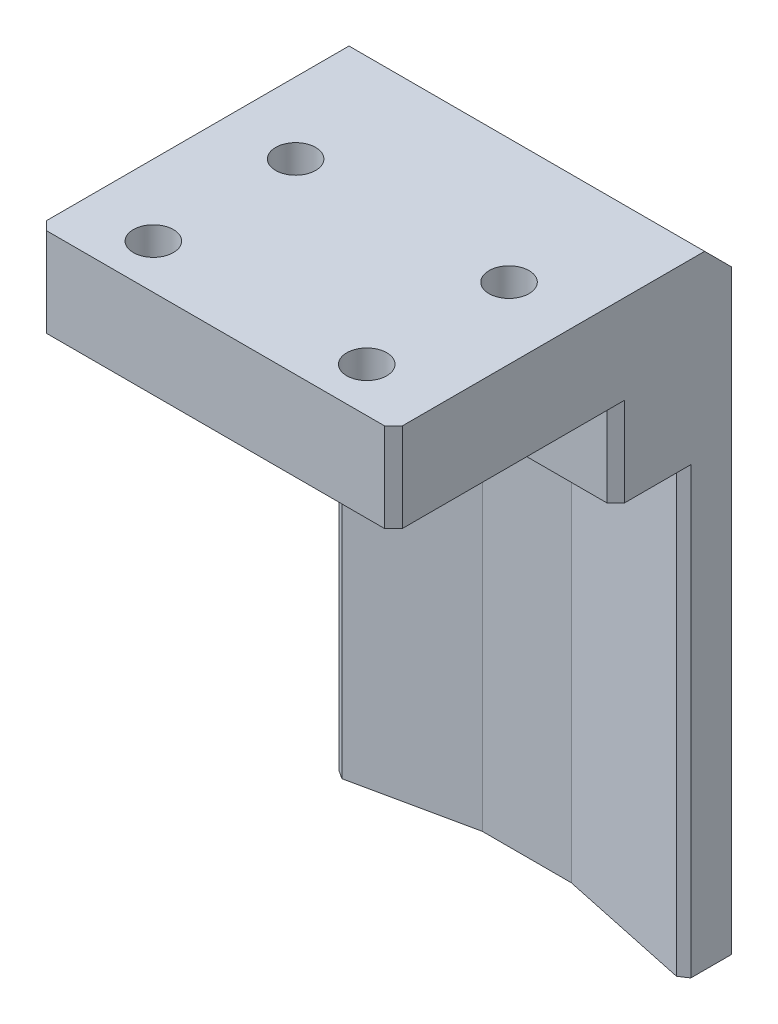
SolidWorks part; units mm, degrees
ref_plane "前视基准面" through (0, 0, 0) normal (0, 0, 1) x (1, 0, 0)
ref_plane "上视基准面" through (0, 0, 0) normal (0, 1, 0) x (1, 0, 0)
ref_plane "右视基准面" through (0, 0, 0) normal (1, 0, 0) x (0, 0, -1)
sketch "草图1" plane through (0, 0, 0) normal (0, 1, 0) x (1, 0, 0)
  line L1 (-20, 7.5) -> (20, 7.5)
  line L2 (-20, 7.5) -> (-20, -7.5)
  line L3 (-20, -7.5) -> (20, -7.5)
  line L4 (20, 7.5) -> (20, -7.5)
  line L5 (-20, 7.5) -> (20, -7.5) construction
  line L6 (-20, -7.5) -> (20, 7.5) construction
  point P0 (0, 0)
  dimension "D1" = 15
  dimension "D2" = 40
extrude "凸台-拉伸1" add sketch "草图1" along normal blind 60
sketch "草图3" plane through (0, 60, 0) normal (0, 1, 0) x (1, 0, 0)
  line L0 (20, -7.5) -> (20, 7.5) construction
  line L1 (-20, 7.5) -> (20, 7.5)
  line L2 (-20, 7.5) -> (-20, -32.5)
  line L3 (-20, -32.5) -> (20, -32.5)
  line L4 (20, 7.5) -> (20, -32.5)
  line L5 (-20, -7.5) -> (20, -7.5) construction
  dimension "D1" = 25
extrude "凸台-拉伸2" add sketch "草图3" along normal blind 10
hole_wizard "M4 六角凹头螺钉的柱形沉头孔1" positions "草图5" profile "草图4" counterbore size "M4" standard "Iso" end condition through all
sketch "草图5" plane through (0, 60, 0) normal (0, -1, 0) x (-1, 0, 0)
  line L0 (0, -32.5) -> (0, 7.5) construction
  line L1 (20, -32.5) -> (-20, -32.5) construction
  line L2 (-20, 7.5) -> (20, 7.5) construction
  point P0 (12, -11.5)
  point P2 (-12, -11.5)
  point P4 (12, -27.5)
  point P6 (-12, -27.5)
  dimension "D1" = 24
  dimension "D2" = 24
  dimension "D3" = 16
  dimension "D4" = 5
sketch "草图4" plane through (-12, 60, 11.5) normal (1, 0, 0) x (0, 0, -1)
  line L0 (0, 0) -> (0, 10)
  line L1 (0, 10) -> (2.25, 10)
  line L3 (2.25, 10) -> (2.25, 4.4)
  line L4 (2.25, 4.4) -> (4, 4.4)
  line L5 (4, 4.4) -> (4, 0)
  line L7 (4, 0) -> (0, 0)
  line L11 (0, -6.35) -> (0, 107.95) construction
  dimension "通孔孔直径" = 4.5
  dimension "通孔孔深度" = 10
  dimension "柱形沉头孔直径" = 8
  dimension "柱形沉头孔深度" = 4.4
chamfer "倒角1" distance 5 angle 45 1 edges at (0, 70, -7.5)
chamfer "倒角2" distance 2 angle 45 2 edges at (20, 32.5, -7.5) (-20, 32.5, -7.5)
sketch "草图7" plane through (0, 0, 0) normal (0, -1, 0) x (1, 0, 0)
  line L0 (-24.6466, 36.5) -> (28.5178, 36.5) construction
  line L1 (18, -7.5) -> (-18, -7.5) construction
  line L2 (0, -7.5) -> (0, 36.5) construction
  line L3 (0, -3.5) -> (25.3434, -3.5) construction
  line L4 (-6, -3.5) -> (4, -3.5)
  line L5 (-6, -3.5) -> (-23.0021, 0.1139)
  line L6 (4, -3.5) -> (25.4647, 1.0625)
  line L7 (-23.0021, 0.1139) -> (-23.0021, 11.878)
  line L8 (-23.0021, 11.878) -> (25.4647, 11.878)
  line L9 (25.4647, 11.878) -> (25.4647, 1.0625)
  dimension "D2" = 12
  dimension "D1" = 44
  dimension "D3" = 4
  dimension "D4" = 10
  dimension "D5" = 6
  dimension "D6" = 12
extrude "切除-拉伸2" cut sketch "草图7" against normal blind 50
chamfer "倒角3" distance 1 angle 45 2 edges at (-20, 25, -0.5242) (20, 25, -0.0991)
sketch "草图8" plane through (0, 50, 0) normal (0, -1, 0) x (1, 0, 0)
  line L0 (0, 7.5) -> (0, -7.5) construction
  line L1 (-20, 7.5) -> (20, 7.5) construction
  line L2 (18, -7.5) -> (-18, -7.5) construction
  line L3 (-10, 7.5) -> (-5, 2.5)
  line L4 (-5, 2.5) -> (5, 2.5)
  line L5 (5, 2.5) -> (10, 7.5)
  line L6 (10, 7.5) -> (-10, 7.5)
  line L7 (-20, 7.5) -> (-12, 7.5) construction
  dimension "D1" = 5
  dimension "D2" = 10
  dimension "D3" = 5
  dimension "D4" = 45
extrude "切除-拉伸3" cut sketch "草图8" against normal up to surface (10 mm away) up to face at (12, 60, 23.5)
chamfer "倒角4" distance 1 angle 45 4 edges at (-20, 65, 32.5) (20, 65, 32.5)
